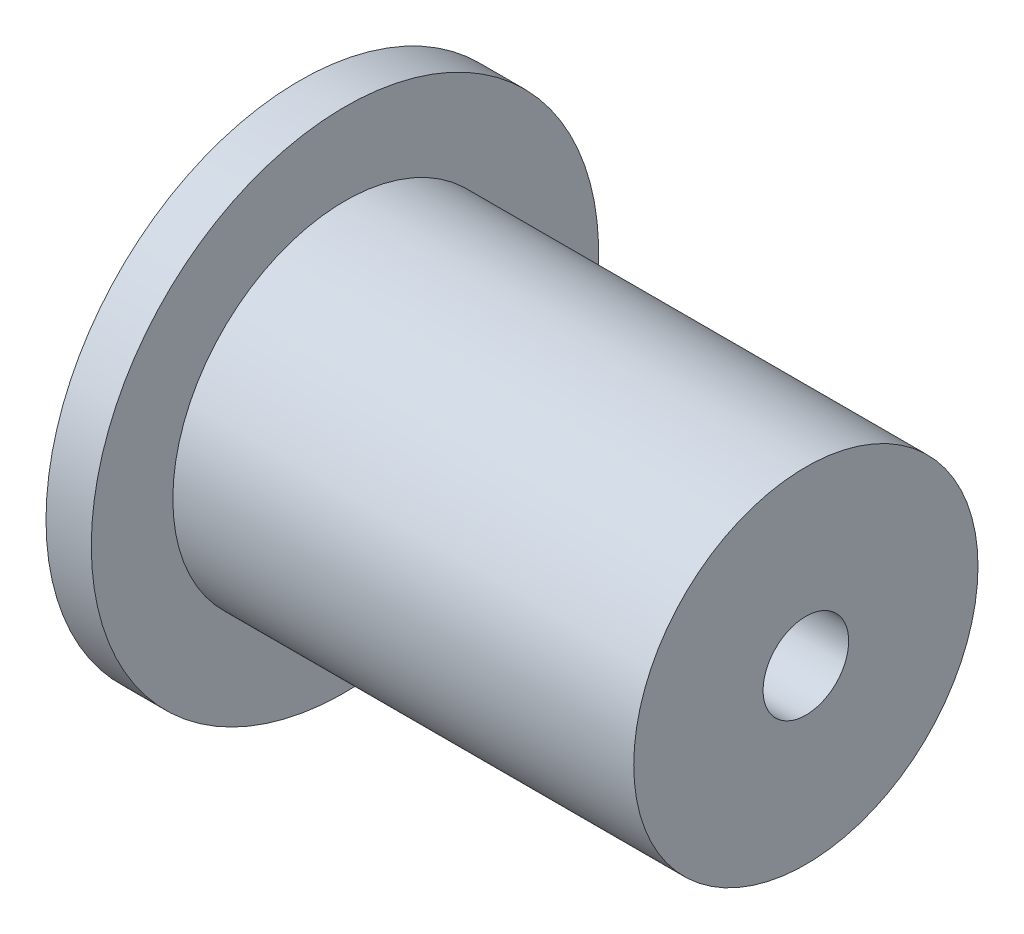
SolidWorks part; units mm, degrees
ref_plane "Front Plane" through (0, 0, 0) normal (0, 0, 1) x (1, 0, 0)
ref_plane "Top Plane" through (0, 0, 0) normal (0, 1, 0) x (1, 0, 0)
ref_plane "Right Plane" through (0, 0, 0) normal (1, 0, 0) x (0, 0, -1)
sketch "Sketch1" plane through (0, 0, 0) normal (0, 0, 1) x (1, 0, 0)
  line L0 (0, 35.56) -> (6.35, 35.56)
  line L1 (6.35, 35.56) -> (6.35, 24.13)
  line L8 (48.1, 15.24) -> (22.7, 15.24)
  line L9 (22.7, 15.24) -> (22.7, 16.002)
  line L10 (22.7, 16.002) -> (12.7, 16.002)
  line L11 (12.7, 16.002) -> (12.7, 18.542)
  line L12 (12.7, 18.542) -> (0, 18.542)
  line L13 (0, 18.542) -> (0, 35.56)
  line L16 (0, 0) -> (18.9296, 0) construction
  line L18 (6.35, 24.13) -> (70.96, 24.13)
  line L21 (70.96, 24.13) -> (70.96, 6)
  line L22 (70.96, 6) -> (60.8, 6)
  line L23 (48.1, 12.7) -> (48.1, 15.24)
  line L24 (48.1, 12.7) -> (60.8, 12.7)
  line L25 (60.8, 12.7) -> (60.8, 6)
  point P19 (9.4648, 0)
  dimension "D2" = 10
  dimension "D3" = 25.4
  dimension "D1" = 16.002
  dimension "D5" = 15.24
  dimension "D8" = 6.35
  dimension "D9" = 35.56
  dimension "D16" = 12.7
  dimension "D11" = 24.13
  dimension "D4" = 6
  dimension "D6" = 2.54
  dimension "D7" = 12.7
  dimension "D10" = 10.16
  dimension "D12" = 2.54
revolve "Revolve1" add sketch "Sketch1" angle 360 about L16
ref_plane "Plane1" through (3.523, 0, 0) normal (-1, 0, 0) x (0, 0, 1)
sketch "Sketch2" plane through (3.523, 0, 0) normal (-1, 0, 0) x (0, 0, 1)
  point P0 (0, 0)
ref_plane "Plane2" through (0, 0, -24.13) normal (0, 0, -1) x (-1, 0, 0)
sketch "Sketch3" plane through (0, 0, -24.13) normal (0, 0, -1) x (-1, 0, 0)
  line L0 (0, 0) -> (-0.348, 0) construction
  line L1 (-6.698, 25.4) -> (-0.348, 25.4)
  line L2 (-6.698, 25.4) -> (-6.698, -25.4)
  line L3 (-6.698, -25.4) -> (-0.348, -25.4)
  line L4 (-0.348, 25.4) -> (-0.348, -25.4)
  line L5 (-3.523, 0) -> (-3.523, 25.4) construction
  point P4 (0, 0)
  point P8 (-3.523, 0)
  dimension "D1" = 50.8
  dimension "D2" = 6.35
sketch "Sketch6" plane through (0, 0, 0) normal (-1, 0, 0) x (0, 0, 1)
  circle A0 centre (0, 0) radius 20.3812
  circle A1 centre (0, 0) radius 22.9212
  dimension "D2" = 40.7624
  dimension "D1" = 2.54
extrude "Cut-Extrude2" cut sketch "Sketch6" against normal blind 1.3462
equation "\"bearing_radius\"= 0.629921"
equation "\"bearing_width\"=0.393701"
equation "\"D2@Sketch1\"=\"bearing_width\""
equation "\"kero_radius\"=0.334in"
equation "\"lox_radius\"=0.23622in"
equation "\"Cavity_width\"=0.031in"
equation "\"tooth_width\"=0.01in"
equation "\"cavity_depth\"=0.031in"
equation "\"seal_step\"=0.01in"
equation "\"purge_length\"=0.04in"
equation "\"insert_radius\" = 0.6in"
equation "\"recycle_groove width\" = 0.06in"
equation "\"recycle_groove_depth\" = 0.06in"
equation "\"N2_purge_width\"= .06in"
equation "\"N2_purge_depth\"= .06in"
equation "\"drain_width\"= .06in"
equation "\"drain_depth\"= .06in"
equation "\"radial_clearance\"= .002in"
equation "\"IPS_flange_width\"= .25in"
equation "\"IPS_flange_radius\" = 1.4in"
equation "\"IPS_LOX_male_radius\"= .9in"
equation "\"IPS_Kero_male_radius\" = .9in"
equation "\"IPS_radius\"= .95in"
equation "\"D5@Sketch1\"=\"insert_radius\""
equation "\"InsertLength\"= 1in"
equation "\"D3@Sketch1\"=\"InsertLength\""
equation "\"D8@Sketch1\"=\"IPS_flange_width\""
equation "\"D9@Sketch1\"=\"IPS_flange_radius\""
equation "\"D11@Sketch1\"=\"IPS_radius\""
equation "\"lox_side_oring_ID\"=1.60482"
equation "\"D2@Sketch6\"=\"lox_side_oring_ID\""
equation "\"lox_oring_depth\"=0.053"
equation "\"D1@Cut-Extrude2\"=\"lox_oring_depth\""
equation "\"D4@Sketch1\"=\"lox_radius\""
equation "\"D10@Sketch1\"=.4"
